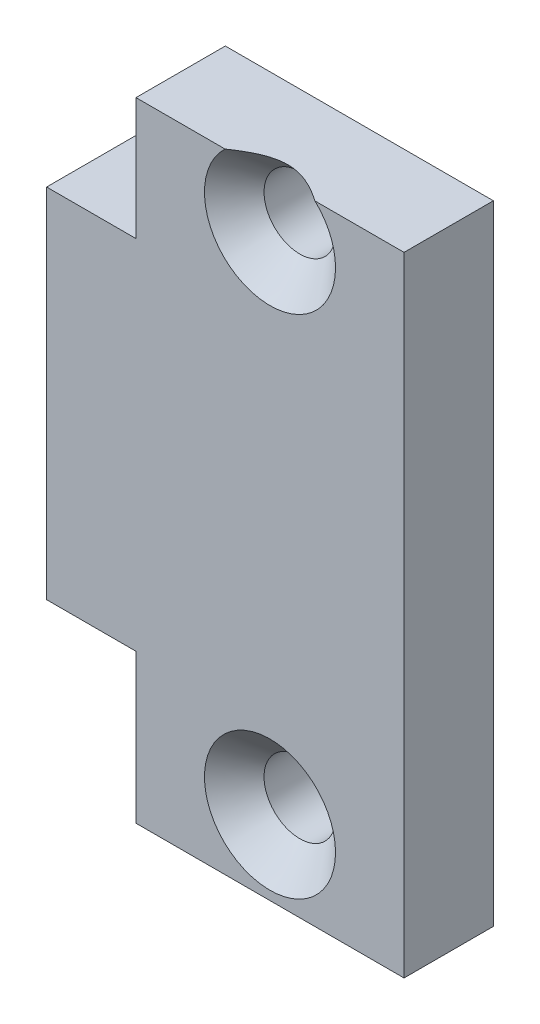
SolidWorks part; units mm, degrees
material "ABS"
ref_plane "Front Plane" through (0, 0, 0) normal (0, 0, 1) x (1, 0, 0)
ref_plane "Top Plane" through (0, 0, 0) normal (0, 1, 0) x (1, 0, 0)
ref_plane "Right Plane" through (0, 0, 0) normal (1, 0, 0) x (0, 0, -1)
sketch "Sketch1" plane through (0, 0, 0) normal (0, 0, 1) x (1, 0, 0)
  line L0 (0, 11) -> (0, -11) construction
  line L1 (-4.5, -11) -> (4.5, -11)
  line L2 (-4.5, -11) -> (-4.5, 11)
  line L3 (-4.5, 11) -> (4.5, 11)
  line L4 (4.5, -11) -> (4.5, 11)
  line L5 (-4.5, -11) -> (4.5, 11) construction
  line L6 (-4.5, 11) -> (4.5, -11) construction
  point P0 (0, 0)
  dimension "D1" = 22
  dimension "D2" = 9
extrude "Boss-Extrude1" add sketch "Sketch1" along normal blind 3
hole_wizard "CSK for M2 Flat Head Machine Screw1" positions "Sketch3" profile "Sketch2" countersink size "M2" standard "ANSI Metric"
sketch "Sketch3" plane through (0, 0, 3) normal (0, 0, 1) x (1, 0, 0)
  line L0 (0, 8.5) -> (0, 0) construction
  line L1 (0, 0) -> (0, -8.5) construction
  point P0 (0, 8.5)
  point P2 (0, -8.5)
  dimension "D1" = 17
sketch "Sketch2" plane through (0, 8.5, 3) normal (1, 0, 0) x (0, -1, 0)
  line L0 (0, 0) -> (0, 10.721)
  line L1 (0, 10.721) -> (1.2, 10)
  line L2 (1.2, 10) -> (1.2, 1)
  line L3 (1.2, 1) -> (2.2, 0)
  line L5 (2.2, 0) -> (0, 0)
  line L6 (-1.2, 1) -> (-2.2, 0) construction
  line L10 (0, 10.721) -> (-1.2, 10) construction
  line L11 (0, -6.35) -> (0, 107.95) construction
  dimension "Hole Dia." = 2.4
  dimension "Hole Depth" = 10
  dimension "Near C'Sink Dia." = 4.4
  dimension "Near C'Sink Angle" = 90
  dimension "Drill Angle" = 118
sketch "Sketch4" plane through (-4.5, 0, 0) normal (-1, 0, 0) x (0, 0, 1)
  line L0 (3, 6) -> (-2, 6)
  line L1 (3, 11) -> (3, -11) construction
  line L2 (0, 11) -> (0, -11) construction
  line L3 (0, 3.7987) -> (0, -3.7987)
  line L4 (0, 0) -> (3, 0) construction
  line L5 (-2, -6) -> (3, -6)
  line L6 (3, -6) -> (3, 6)
  line L7 (0, 0) -> (-4.9, 0) construction
  line L8 (-2, 6) -> (-2, 5.48)
  line L9 (-2, -5.48) -> (-2, -6)
  arc A0 (-2, 5.48) -> (0, 3.7987) centre (-4.9, 0) cw
  arc A1 (0, -3.7987) -> (-2, -5.48) centre (-4.9, 0) cw
  dimension "D1" = 6.2
  dimension "D2" = 12
  dimension "D3" = 4.9
  dimension "D4" = 2
extrude "Boss-Extrude2" add sketch "Sketch4" along normal blind 3
sketch "Sketch5" plane through (0, 11, 0) normal (0, 1, 0) x (1, 0, 0)
  line L0 (-4.5, -3) -> (-4.5, 0) construction
  line L1 (-4.5, 0) -> (4.5, 0)
  line L2 (-4.5, 0) -> (-4.5, -3)
  line L3 (-4.5, -3) -> (4.5, -3)
  line L4 (4.5, 0) -> (4.5, -3)
  line L5 (4.5, -3) -> (-4.5, -3) construction
extrude "Cut-Extrude1" cut sketch "Sketch5" against normal blind 0.9
